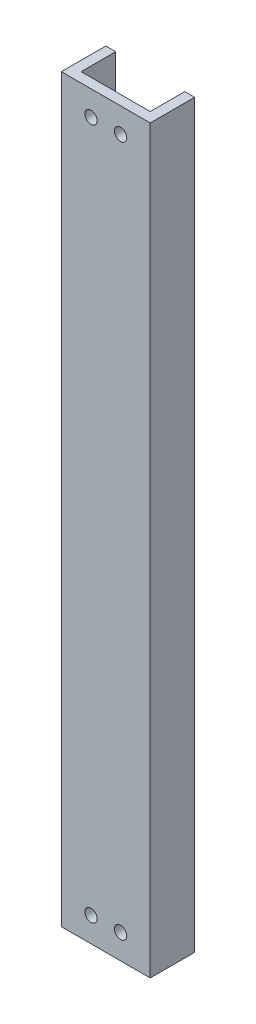
SolidWorks part; units mm, degrees
ref_plane "Front Plane" through (0, 0, 0) normal (0, 0, 1) x (1, 0, 0)
ref_plane "Top Plane" through (0, 0, 0) normal (0, 1, 0) x (1, 0, 0)
ref_plane "Right Plane" through (0, 0, 0) normal (1, 0, 0) x (0, 0, -1)
sketch "Sketch1" plane through (0, 0, 0) normal (0, 1, 0) x (1, 0, 0)
  line L0 (-7, 4.5) -> (-7, -2.5)
  line L2 (-9, 4.5) -> (-9, -4.5)
  line L3 (-9, -4.5) -> (9, -4.5)
  line L4 (9, 4.5) -> (9, -4.5)
  line L5 (-9, 4.5) -> (9, -4.5) construction
  line L6 (-9, -4.5) -> (9, 4.5) construction
  line L7 (-7, -2.5) -> (7, -2.5)
  line L8 (7, 4.5) -> (7, -2.5)
  line L9 (-9, 4.5) -> (-7, 4.5)
  line L10 (9, 4.5) -> (7, 4.5)
  point P0 (0, 0)
  dimension "D1" = 18
  dimension "D2" = 9
  dimension "D4" = 14
  dimension "D5" = 9
  dimension "D3" = 2
extrude "Boss-Extrude1" add sketch "Sketch1" along normal blind 150
sketch "Sketch2" plane through (0, 0, 2.5) normal (0, 0, -1) x (-1, 0, 0)
  line L0 (0, 150) -> (0, 0) construction
  line L1 (-7, 150) -> (7, 150) construction
  line L2 (-7, 2) -> (7, 2) construction
  line L3 (-7, 150) -> (-7, 0) construction
  line L4 (7, 150) -> (7, 0) construction
  line L5 (-7, 0) -> (7, 0) construction
  line L6 (-9, 75) -> (9, 75) construction
  line L7 (-9, 150) -> (-9, 0) construction
  line L8 (9, 150) -> (9, 0) construction
  circle A0 centre (-3, 5) radius 1.25
  circle A1 centre (3, 5) radius 1.25
  circle A2 centre (3, 145) radius 1.25
  circle A3 centre (-3, 145) radius 1.25
  dimension "D2" = 2.5
  dimension "D3" = 2.5
  dimension "D1" = 2
  dimension "D4" = 6
  dimension "D5" = 3
  dimension "D6" = 3
  dimension "D7" = 3
extrude "Cut-Extrude1" cut sketch "Sketch2" against normal blind 10
